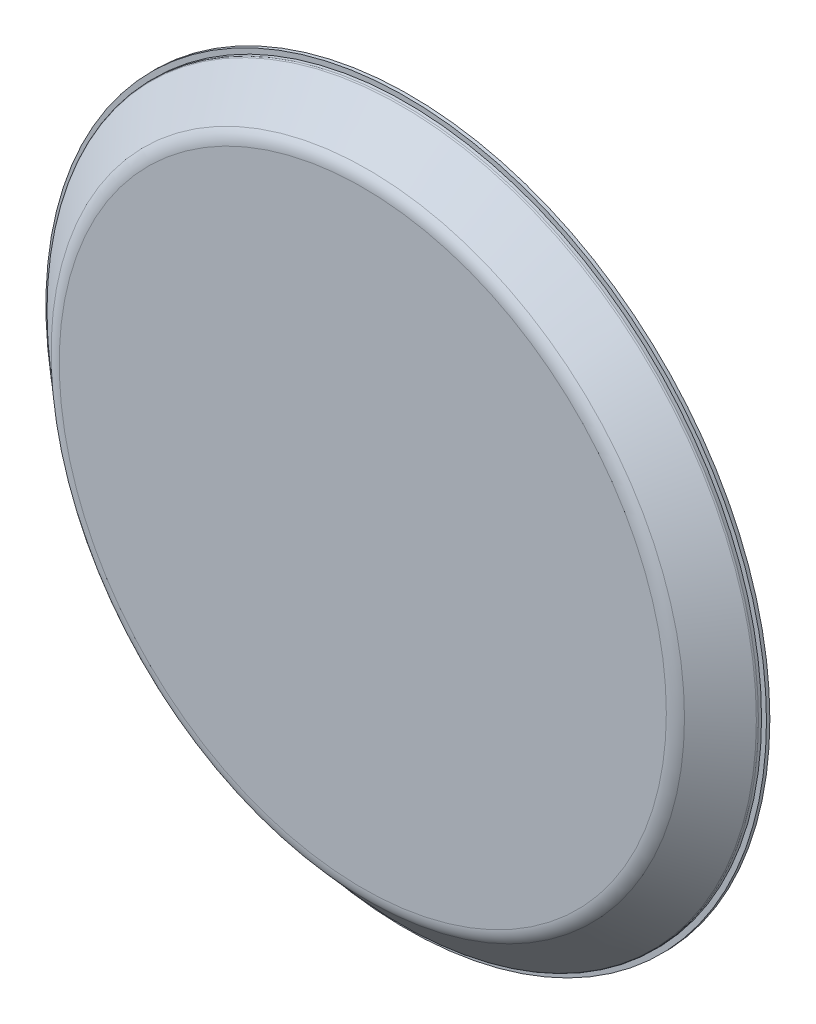
SolidWorks part; units mm, degrees
ref_plane "Front Plane" through (0, 0, 0) normal (0, 0, 1) x (1, 0, 0)
ref_plane "Top Plane" through (0, 0, 0) normal (0, 1, 0) x (1, 0, 0)
ref_plane "Right Plane" through (0, 0, 0) normal (1, 0, 0) x (0, 0, -1)
sketch "Sketch1" plane through (0, 0, 0) normal (1, 0, 0) x (0, 0, -1)
  line L0 (0, 70.8819) -> (0, -77.1698) construction
  line L1 (0.2, 18.2509) -> (0.3685, 18.2536)
  line L2 (0.3685, 18.2536) -> (0.3685, 17.5642)
  line L3 (-1.2984, 15.6582) -> (0.3431, 17.4976)
  line L4 (-1.4, 15.3919) -> (-1.4, 0)
  line L5 (-1.4, 0) -> (-2, 0)
  line L6 (-2, 0) -> (-2, 15.3776)
  line L7 (-1.7461, 16.0434) -> (-0.0297, 17.9668)
  line L8 (-10.6441, 0) -> (9.8244, 0) construction
  line L10 (0.0445, 18.0002) -> (0.2, 18.0009)
  line L11 (0.2, 18.0009) -> (0.2, 18.2509)
  line L20 (-2, 20.3) -> (-2, -6.7828) construction
  arc A0 (-2, 15.3776) -> (-1.7461, 16.0434) centre (-1, 15.3776) cw
  arc A1 (-1.2984, 15.6582) -> (-1.4, 15.3919) centre (-1, 15.3919) ccw
  arc A2 (-0.0297, 17.9668) -> (0.0445, 18.0002) centre (0.045, 17.9002) cw
  arc A3 (0.3685, 17.5642) -> (0.3431, 17.4976) centre (0.2685, 17.5642) cw
  point P19 (0, 18)
  dimension "D3" = 1
  dimension "D4" = 0.4
  dimension "D7" = 0.1
  dimension "D8" = 0.1
  dimension "D1" = 0.2
  dimension "D2" = 0.6
  dimension "D5" = 0.25
  dimension "D6" = 2
revolve "Revolve1" add sketch "Sketch1" angle 360 about L8
